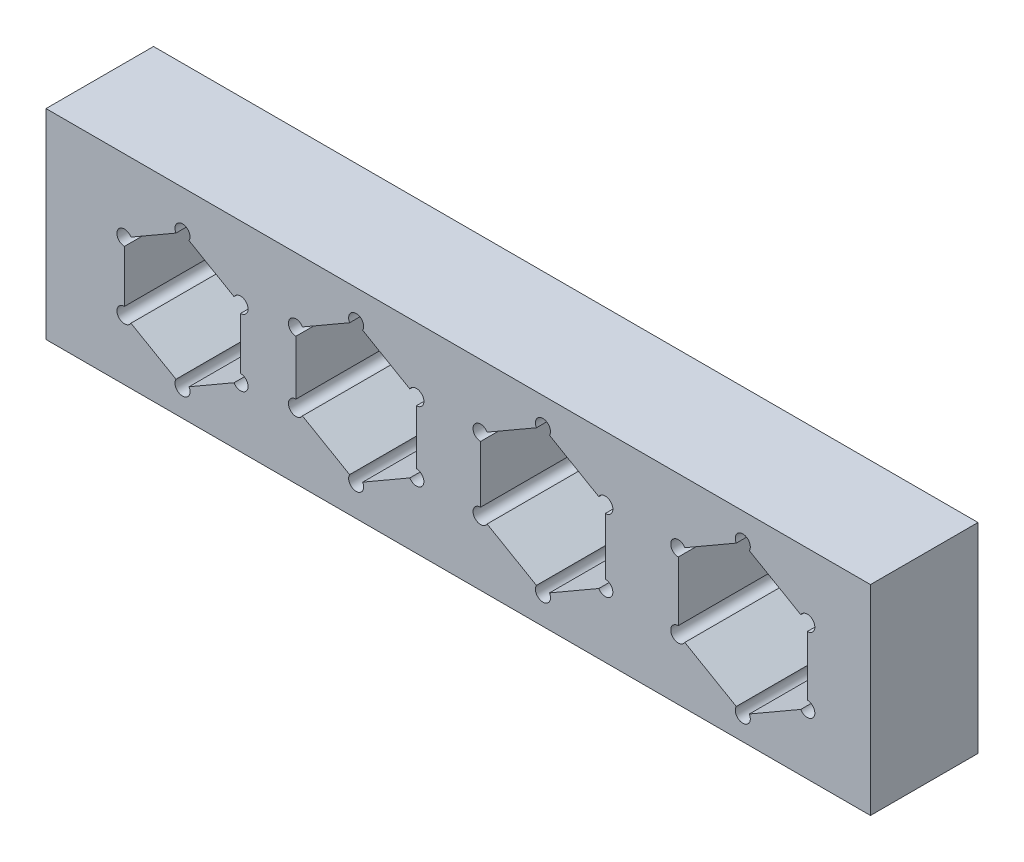
SolidWorks part; units mm, degrees
ref_plane "Front Plane" through (0, 0, 0) normal (0, 0, 1) x (1, 0, 0)
ref_plane "Top Plane" through (0, 0, 0) normal (0, 1, 0) x (1, 0, 0)
ref_plane "Right Plane" through (0, 0, 0) normal (1, 0, 0) x (0, 0, -1)
sketch "Sketch1" plane through (0, 0, 0) normal (0, 0, 1) x (1, 0, 0)
  line L0 (0, 3.2332) -> (-0.3031, 3.0582) construction
  line L1 (-8.3779, 2.6309) -> (-10.4717, 1.4221)
  line L2 (-10.7748, 0.8971) -> (-10.7748, -1.5206)
  line L3 (-10.4717, -2.0456) -> (-8.3779, -3.2545)
  line L4 (-7.7717, -3.2545) -> (-5.6779, -2.0456)
  line L5 (-5.3748, -1.5206) -> (-5.3748, 0.8971)
  line L6 (-5.6779, 1.4221) -> (-7.7717, 2.6309)
  line L7 (-0.3031, 3.0582) -> (-2.4969, 1.7916)
  line L8 (-2.8, 1.2666) -> (-2.8, -1.2666)
  line L9 (-2.4969, -1.7916) -> (-0.3031, -3.0582)
  line L10 (0.3031, -3.0582) -> (2.4969, -1.7916)
  line L11 (2.8, -1.2666) -> (2.8, 1.2666)
  line L12 (2.4969, 1.7916) -> (0.3031, 3.0582)
  line L13 (8.3834, 3.1719) -> (6.0896, 1.8476)
  line L14 (5.7865, 1.3226) -> (5.7865, -1.326)
  line L15 (6.0896, -1.851) -> (8.3834, -3.1753)
  line L16 (8.9896, -3.1753) -> (11.2834, -1.851)
  line L17 (11.5865, -1.326) -> (11.5865, 1.3226)
  line L18 (11.2834, 1.8476) -> (8.9896, 3.1719)
  line L19 (17.676, 3.1726) -> (15.2823, 1.7906)
  line L20 (14.9792, 1.2656) -> (14.9792, -1.4985)
  line L21 (15.2823, -2.0235) -> (17.676, -3.4056)
  line L22 (18.2823, -3.4056) -> (20.676, -2.0235)
  line L23 (20.9792, -1.4985) -> (20.9792, 1.2656)
  line L24 (20.676, 1.7906) -> (18.2823, 3.1726)
  line L25 (0.3031, 3.0582) -> (0, 3.2332) construction
  line L26 (2.8, 1.6166) -> (2.4969, 1.7916) construction
  line L27 (2.8, 1.2666) -> (2.8, 1.6166) construction
  line L28 (2.8, -1.6166) -> (2.8, -1.2666) construction
  line L29 (2.4969, -1.7916) -> (2.8, -1.6166) construction
  line L30 (0, -3.2332) -> (0.3031, -3.0582) construction
  line L31 (-0.3031, -3.0582) -> (0, -3.2332) construction
  line L32 (-2.8, -1.6166) -> (-2.4969, -1.7916) construction
  line L33 (-2.8, -1.2666) -> (-2.8, -1.6166) construction
  line L34 (-2.8, 1.6166) -> (-2.8, 1.2666) construction
  line L35 (-2.4969, 1.7916) -> (-2.8, 1.6166) construction
  line L36 (-8.0748, 2.8059) -> (-8.3779, 2.6309) construction
  line L37 (-7.7717, 2.6309) -> (-8.0748, 2.8059) construction
  line L38 (-5.3748, 1.2471) -> (-5.6779, 1.4221) construction
  line L39 (-5.3748, 0.8971) -> (-5.3748, 1.2471) construction
  line L40 (-5.6779, -2.0456) -> (-5.3748, -1.8706) construction
  line L41 (-5.3748, -1.8706) -> (-5.3748, -1.5206) construction
  line L42 (-8.3779, -3.2545) -> (-8.0748, -3.4295) construction
  line L43 (-8.0748, -3.4295) -> (-7.7717, -3.2545) construction
  line L44 (-10.7748, -1.5206) -> (-10.7748, -1.8706) construction
  line L45 (-10.7748, -1.8706) -> (-10.4717, -2.0456) construction
  line L46 (-10.4717, 1.4221) -> (-10.7748, 1.2471) construction
  line L47 (-10.7748, 1.2471) -> (-10.7748, 0.8971) construction
  line L48 (8.6865, 3.3469) -> (8.3834, 3.1719) construction
  line L49 (8.9896, 3.1719) -> (8.6865, 3.3469) construction
  line L50 (11.5865, 1.3226) -> (11.5865, 1.6726) construction
  line L51 (11.5865, 1.6726) -> (11.2834, 1.8476) construction
  line L52 (11.2834, -1.851) -> (11.5865, -1.676) construction
  line L53 (11.5865, -1.676) -> (11.5865, -1.326) construction
  line L54 (8.3834, -3.1753) -> (8.6865, -3.3503) construction
  line L55 (8.6865, -3.3503) -> (8.9896, -3.1753) construction
  line L56 (5.7865, -1.326) -> (5.7865, -1.676) construction
  line L57 (5.7865, -1.676) -> (6.0896, -1.851) construction
  line L58 (6.0896, 1.8476) -> (5.7865, 1.6726) construction
  line L59 (5.7865, 1.6726) -> (5.7865, 1.3226) construction
  line L60 (14.9792, 1.6156) -> (14.9792, 1.2656) construction
  line L61 (15.2823, 1.7906) -> (14.9792, 1.6156) construction
  line L62 (17.9792, 3.3476) -> (17.676, 3.1726) construction
  line L63 (18.2823, 3.1726) -> (17.9792, 3.3476) construction
  line L64 (20.9792, 1.6156) -> (20.676, 1.7906) construction
  line L65 (20.9792, 1.2656) -> (20.9792, 1.6156) construction
  line L66 (20.676, -2.0235) -> (20.9792, -1.8485) construction
  line L67 (20.9792, -1.8485) -> (20.9792, -1.4985) construction
  line L68 (17.9792, -3.5806) -> (18.2823, -3.4056) construction
  line L69 (17.676, -3.4056) -> (17.9792, -3.5806) construction
  line L70 (14.9792, -1.4985) -> (14.9792, -1.8485) construction
  line L71 (14.9792, -1.8485) -> (15.2823, -2.0235) construction
  line L73 (-14.4221, 4.6235) -> (23.9165, 4.6235)
  line L74 (-14.4221, 4.6235) -> (-14.4221, -4.6774)
  line L75 (-14.4221, -4.6774) -> (23.9165, -4.6774)
  line L76 (23.9165, 4.6235) -> (23.9165, -4.6774)
  circle A0 centre (-8.0748, -0.3118) radius 2.7 construction
  circle A1 centre (0, 0) radius 2.8 construction
  circle A2 centre (8.6865, -0.0017) radius 2.9 construction
  circle A3 centre (17.9792, -0.1165) radius 3 construction
  arc A4 (-7.7717, 2.6309) -> (-8.3779, 2.6309) centre (-8.0748, 2.8059) ccw
  arc A5 (-5.3748, 0.8971) -> (-5.6779, 1.4221) centre (-5.3748, 1.2471) ccw
  arc A6 (-5.6779, -2.0456) -> (-5.3748, -1.5206) centre (-5.3748, -1.8706) ccw
  arc A7 (-8.3779, -3.2545) -> (-7.7717, -3.2545) centre (-8.0748, -3.4295) ccw
  arc A8 (-10.7748, -1.5206) -> (-10.4717, -2.0456) centre (-10.7748, -1.8706) ccw
  arc A9 (-10.4717, 1.4221) -> (-10.7748, 0.8971) centre (-10.7748, 1.2471) ccw
  arc A10 (0.3031, 3.0582) -> (-0.3031, 3.0582) centre (0, 3.2332) ccw
  arc A11 (2.8, 1.2666) -> (2.4969, 1.7916) centre (2.8, 1.6166) ccw
  arc A12 (2.4969, -1.7916) -> (2.8, -1.2666) centre (2.8, -1.6166) ccw
  arc A13 (-0.3031, -3.0582) -> (0.3031, -3.0582) centre (0, -3.2332) ccw
  arc A14 (-2.8, -1.2666) -> (-2.4969, -1.7916) centre (-2.8, -1.6166) ccw
  arc A15 (-2.4969, 1.7916) -> (-2.8, 1.2666) centre (-2.8, 1.6166) ccw
  arc A16 (8.9896, 3.1719) -> (8.3834, 3.1719) centre (8.6865, 3.3469) ccw
  arc A17 (11.5865, 1.3226) -> (11.2834, 1.8476) centre (11.5865, 1.6726) ccw
  arc A18 (11.2834, -1.851) -> (11.5865, -1.326) centre (11.5865, -1.676) ccw
  arc A19 (8.3834, -3.1753) -> (8.9896, -3.1753) centre (8.6865, -3.3503) ccw
  arc A20 (5.7865, -1.326) -> (6.0896, -1.851) centre (5.7865, -1.676) ccw
  arc A21 (6.0896, 1.8476) -> (5.7865, 1.3226) centre (5.7865, 1.6726) ccw
  arc A22 (18.2823, 3.1726) -> (17.676, 3.1726) centre (17.9792, 3.3476) ccw
  arc A23 (20.9792, 1.2656) -> (20.676, 1.7906) centre (20.9792, 1.6156) ccw
  arc A24 (20.676, -2.0235) -> (20.9792, -1.4985) centre (20.9792, -1.8485) ccw
  arc A25 (17.676, -3.4056) -> (18.2823, -3.4056) centre (17.9792, -3.5806) ccw
  arc A26 (14.9792, -1.4985) -> (15.2823, -2.0235) centre (14.9792, -1.8485) ccw
  arc A27 (15.2823, 1.7906) -> (14.9792, 1.2656) centre (14.9792, 1.6156) ccw
  arc A28 (-0.3031, 3.0582) -> (0.3031, 3.0582) centre (0, 3.2332) ccw construction
  arc A29 (2.4969, 1.7916) -> (2.8, 1.2666) centre (2.8, 1.6166) ccw construction
  arc A30 (2.8, -1.2666) -> (2.4969, -1.7916) centre (2.8, -1.6166) ccw construction
  arc A31 (0.3031, -3.0582) -> (-0.3031, -3.0582) centre (0, -3.2332) ccw construction
  arc A32 (-2.4969, -1.7916) -> (-2.8, -1.2666) centre (-2.8, -1.6166) ccw construction
  arc A33 (-2.8, 1.2666) -> (-2.4969, 1.7916) centre (-2.8, 1.6166) ccw construction
  arc A34 (-8.3779, 2.6309) -> (-7.7717, 2.6309) centre (-8.0748, 2.8059) ccw construction
  arc A35 (-5.6779, 1.4221) -> (-5.3748, 0.8971) centre (-5.3748, 1.2471) ccw construction
  arc A36 (-5.3748, -1.5206) -> (-5.6779, -2.0456) centre (-5.3748, -1.8706) ccw construction
  arc A37 (-7.7717, -3.2545) -> (-8.3779, -3.2545) centre (-8.0748, -3.4295) ccw construction
  arc A38 (-10.4717, -2.0456) -> (-10.7748, -1.5206) centre (-10.7748, -1.8706) ccw construction
  arc A39 (-10.7748, 0.8971) -> (-10.4717, 1.4221) centre (-10.7748, 1.2471) ccw construction
  arc A40 (8.3834, 3.1719) -> (8.9896, 3.1719) centre (8.6865, 3.3469) ccw construction
  arc A41 (11.2834, 1.8476) -> (11.5865, 1.3226) centre (11.5865, 1.6726) ccw construction
  arc A42 (11.5865, -1.326) -> (11.2834, -1.851) centre (11.5865, -1.676) ccw construction
  arc A43 (8.9896, -3.1753) -> (8.3834, -3.1753) centre (8.6865, -3.3503) ccw construction
  arc A44 (6.0896, -1.851) -> (5.7865, -1.326) centre (5.7865, -1.676) ccw construction
  arc A45 (5.7865, 1.3226) -> (6.0896, 1.8476) centre (5.7865, 1.6726) ccw construction
  arc A46 (14.9792, 1.2656) -> (15.2823, 1.7906) centre (14.9792, 1.6156) ccw construction
  arc A47 (17.676, 3.1726) -> (18.2823, 3.1726) centre (17.9792, 3.3476) ccw construction
  arc A48 (20.676, 1.7906) -> (20.9792, 1.2656) centre (20.9792, 1.6156) ccw construction
  arc A49 (20.9792, -1.4985) -> (20.676, -2.0235) centre (20.9792, -1.8485) ccw construction
  arc A50 (18.2823, -3.4056) -> (17.676, -3.4056) centre (17.9792, -3.5806) ccw construction
  arc A51 (15.2823, -2.0235) -> (14.9792, -1.4985) centre (14.9792, -1.8485) ccw construction
  point P47 (-8.0748, -0.3118)
  point P59 (0, 0)
  point P71 (8.6865, -0.0017)
  point P82 (17.9792, -0.1165)
  dimension "D5" = 0.7
  dimension "D7" = 0.7
  dimension "D9" = 0.7
  dimension "D11" = 0.7
  dimension "D1" = 5.4
  dimension "D2" = 5.6
  dimension "D3" = 5.8
  dimension "D4" = 6
  dimension "D6" = 6
  dimension "D8" = 6
  dimension "D10" = 6
  dimension "D12" = 6
extrude "Boss-Extrude1" add sketch "Sketch1" along normal blind 5
